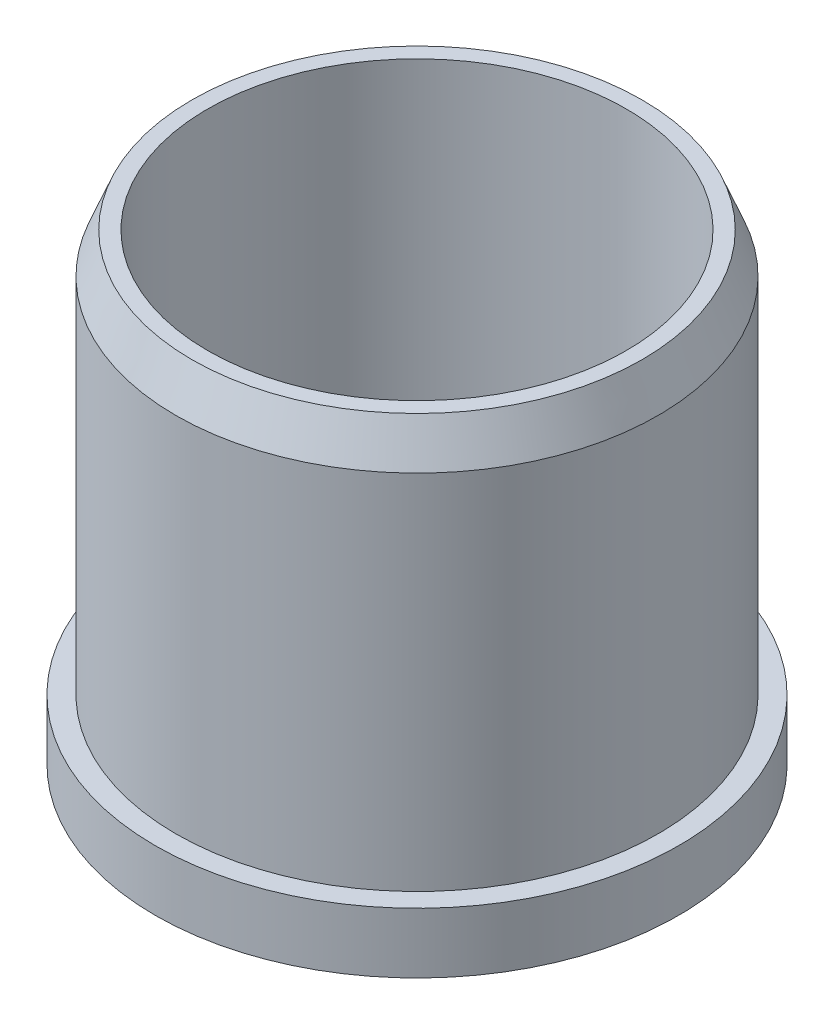
SolidWorks part; units mm, degrees
material "ABS"
ref_plane "Front Plane" through (0, 0, 0) normal (0, 0, 1) x (1, 0, 0)
ref_plane "Top Plane" through (0, 0, 0) normal (0, 1, 0) x (1, 0, 0)
ref_plane "Right Plane" through (0, 0, 0) normal (1, 0, 0) x (0, 0, -1)
sketch "Sketch1" plane through (0, 0, 0) normal (0, 1, 0) x (1, 0, 0)
  line L6 (0, 12.7) -> (0, 33.02)
  circle A0 centre (0, 0) radius 41.275
  circle A1 centre (0, 0) radius 6.5024
  circle A2 centre (0, 0) radius 12.7
  circle A3 centre (0, 0) radius 33.02
  circle A4 centre (0, 22.86) radius 7.62
  circle A5 centre (21.7412, 7.0641) radius 7.62
  circle A6 centre (13.4368, -18.4941) radius 7.62
  circle A7 centre (-13.4368, -18.4941) radius 7.62
  circle A8 centre (-21.7412, 7.0641) radius 7.62
  point P26 (0, 0)
  dimension "D1" = 82.55
  dimension "D2" = 13.0048
  dimension "D6" = 25.4
  dimension "D7" = 66.04
  dimension "D8" = 15.24
  dimension "D9" = 5
extrude "Boss-Extrude1" add sketch "Sketch1" along normal blind 9.525
sketch "Sketch2" plane through (0, 9.525, 0) normal (0, 1, 0) x (1, 0, 0)
  circle A0 centre (0, 0) radius 38.0365
  circle A1 centre (0, 0) radius 33.02
  dimension "D1" = 76.073
  dimension "D2" = 66.04
extrude "Boss-Extrude2" add sketch "Sketch2" along normal blind 63.5
sketch "Sketch3" plane through (0, 9.525, 0) normal (0, 1, 0) x (1, 0, 0)
  circle A0 centre (0, 0) radius 12.7
  circle A2 centre (0, 0) radius 6.5024
  dimension "D1" = 25.4
  dimension "D2" = 13.0048
extrude "Boss-Extrude3" add sketch "Sketch3" along normal blind 15.875
chamfer "Chamfer1" distance 6.35 distance2 2.54 1 edges at (0, 73.025, 38.0365)
sketch "Sketch4" plane through (0, 25.4, 0) normal (0, 1, 0) x (1, 0, 0)
  circle A0 centre (0, 0) radius 12.7
  circle A1 centre (0, 0) radius 6.5024
  dimension "D1" = 25.4
extrude "Boss-Extrude4" add sketch "Sketch4" along normal blind 6.35
fillet "Fillet1" radius 2.54 1 edges at (0, 31.75, 12.7)
